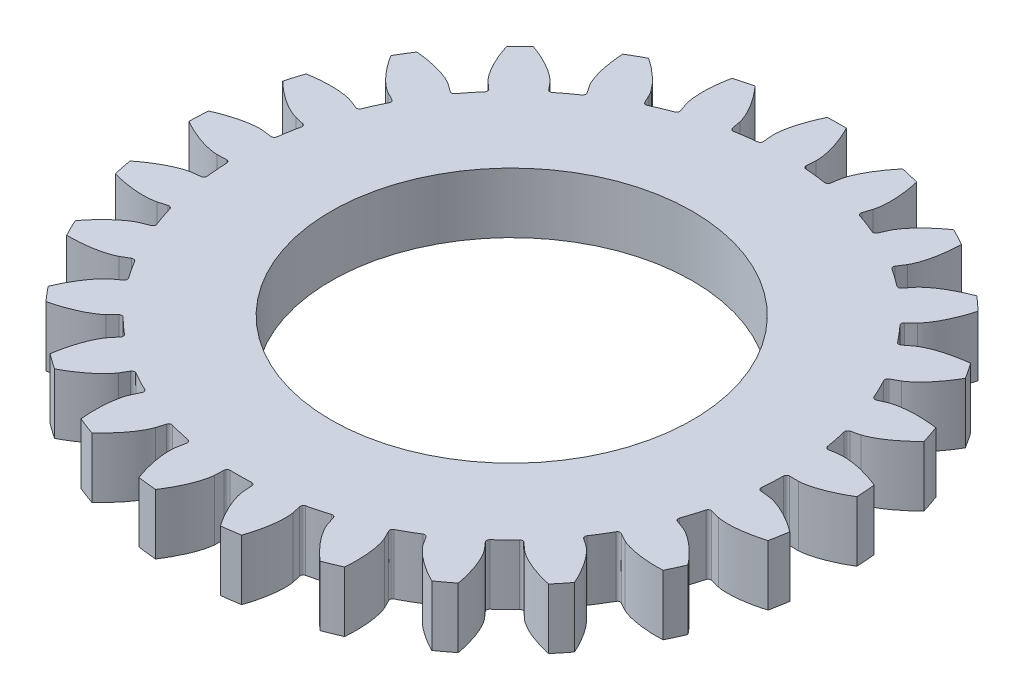
SolidWorks part; units mm, degrees
ref_plane "Front" through (0, 0, 0) normal (0, 0, 1) x (1, 0, 0)
ref_plane "Top" through (0, 0, 0) normal (0, 1, 0) x (1, 0, 0)
ref_plane "Right" through (0, 0, 0) normal (1, 0, 0) x (0, 0, -1)
sketch "Sketch3" plane through (0, 0, 0) normal (0, 1, 0) x (1, 0, 0)
  circle A0 centre (0, 0) radius 27.365
  dimension "D1" = 54.73
extrude "Boss-Extrude2" add sketch "Sketch3" against normal blind 5
sketch "Sketch4" plane through (0, 0, 0) normal (0, 1, 0) x (1, 0, 0)
  line L0 (0, 0) -> (23.8085, 0) construction
  line L1 (0, 0) -> (25.3342, 0.3427) construction
  line L2 (0, 0) -> (27.3317, -1.3487) construction
  line L3 (22.8028, 0) -> (23.8085, 0)
  line L4 (22.7751, -1.1238) -> (27.3317, -1.3487)
  circle A0 centre (0, 0) radius 25.3365
  circle A1 centre (0, 0) radius 23.8085
  circle A2 centre (0, 0) radius 22.8028
  circle A3 centre (0, 0) radius 27.365 construction
  circle A4 centre (0, 0) radius 27.365 construction
  arc A5 (27.3317, -1.3487) -> (27.3337, 1.3084) centre (0, 0) ccw
  spline S0 degree 4 poles (23.8085, 0) (23.8261, 0) (23.8755, 0.0012) (23.9687, 0.0079) (24.1203, 0.0253) (24.4006, 0.0715) (24.821, 0.17) (25.2762, 0.3139) (25.7496, 0.4971) (26.1592, 0.6786) (26.4819, 0.8345) (26.8675, 1.0357) (27.3231, 1.2956) (27.8429, 1.6229) (28.4198, 2.0263) (28.9877, 2.4636) (29.5365, 2.9252) (30.0658, 3.4083) (30.5766, 3.912) (31.0677, 4.433) (31.4823, 4.9056) (31.8241, 5.3176) (32.1044, 5.6717) (32.3185, 5.9503) (32.5396, 6.2494) (32.7342, 6.5191) (33.0063, 6.9125) (33.2008, 7.2047) (33.4934, 7.6571) (33.5905, 7.8234) (33.6939, 7.9901) knots 0 0 0 0 0 0.005377 0.015084 0.028532 0.04661 0.092111 0.146842 0.174209 0.201575 0.228941 0.256307 0.307035 0.361767 0.4165 0.471232 0.525964 0.580697 0.635429 0.690161 0.744894 0.77226 0.799626 0.826992 0.854358 0.881725 0.909091 0.954545 1 1 1 1 1 construction
  spline S1 degree 4 poles (23.8085, 0) (23.8261, 0) (23.8755, 0.0012) (23.9687, 0.0079) (24.1203, 0.0253) (24.4006, 0.0715) (24.821, 0.17) (25.2762, 0.3139) (25.7496, 0.4971) (26.1592, 0.6786) (26.4819, 0.8345) (26.8675, 1.0357) (27.3231, 1.2956) (27.8429, 1.6229) (28.4198, 2.0263) (28.9877, 2.4636) (29.5365, 2.9252) (30.0658, 3.4083) (30.5766, 3.912) (31.0677, 4.433) (31.4823, 4.9056) (31.8241, 5.3176) (32.1044, 5.6717) (32.3185, 5.9503) (32.5396, 6.2494) (32.7342, 6.5191) (32.9093, 6.7723) (33.0022, 6.9089) (33.0476, 6.9765) knots 0 0 0 0 0 0.005377 0.015084 0.028532 0.04661 0.092111 0.146842 0.174209 0.201575 0.228941 0.256307 0.307035 0.361767 0.4165 0.471232 0.525964 0.580697 0.635429 0.690161 0.744894 0.77226 0.799626 0.826992 0.854358 0.881725 0.909091 0.909091 0.909091 0.909091 0.909091
  circle M5 centre (0, 0) radius 27.365
  dimension "D1" = 50.673
  dimension "D2" = 47.617
  dimension "D3" = 45.6057
  dimension "D4" = 3.6
extrude "Cut-Extrude1" cut sketch "Sketch4" against normal blind 5 contours A2 L4 A1 L3 | S1 A1 L4 A0 | S1 A0 L4 M5
fillet "Fillet1" radius 0.2534 1 edges at (22.8028, -2.5, 0)
ref_plane "Plane2" through (0, 0, 0) normal (0.0493, 0, -0.9988) x (-0.9988, 0, -0.0493)
mirror "Mirror2" about plane through (0, 0, 0) normal (0.0493, 0, -0.9988) of "Cut-Extrude1", "Fillet1"
sketch "Sketch5" plane through (0, 0, 0) normal (0, 1, 0) x (1, 0, 0)
  line L0 (22.9428, -2.2698) -> (23.6929, -2.344) construction
  line L1 (23.0548, 0) -> (23.8085, 0) construction
  line L2 (22.9428, -2.2698) -> (23.6929, -2.344)
  line L3 (23.0548, 0) -> (23.8085, 0)
  line L4 (21.6576, -7.9041) -> (22.3656, -8.1625)
  line L5 (22.3305, -5.7335) -> (23.0605, -5.9209)
  line L6 (19.0115, -13.0418) -> (19.633, -13.4682)
  line L7 (20.2031, -11.1067) -> (20.8636, -11.4698)
  line L8 (15.1708, -17.36) -> (15.6668, -17.9276)
  line L9 (16.8062, -15.7821) -> (17.3557, -16.2981)
  line L10 (10.377, -20.5875) -> (10.7162, -21.2605)
  line L11 (12.3534, -19.4658) -> (12.7572, -20.1022)
  line L12 (4.9311, -22.5213) -> (5.0923, -23.2576)
  line L13 (7.1243, -21.9264) -> (7.3572, -22.6433)
  line L14 (-0.8247, -23.0401) -> (-0.8516, -23.7933)
  line L15 (1.4476, -23.0093) -> (1.4949, -23.7615)
  line L16 (-6.5286, -22.1111) -> (-6.742, -22.834)
  line L17 (-4.32, -22.6465) -> (-4.4613, -23.3868)
  line L18 (-11.8223, -19.7929) -> (-12.2088, -20.4399)
  line L19 (-9.8163, -20.8606) -> (-10.1372, -21.5426)
  line L20 (-16.3732, -16.2309) -> (-16.9085, -16.7616)
  line L21 (-14.6957, -17.764) -> (-15.1761, -18.3448)
  line L22 (-19.8953, -11.6492) -> (-20.5457, -12.03)
  line L23 (-18.6517, -13.5513) -> (-19.2615, -13.9943)
  line L24 (-22.1672, -6.3354) -> (-22.8919, -6.5426)
  line L25 (-21.4358, -8.487) -> (-22.1366, -8.7645)
  line L26 (-23.0464, -0.6236) -> (-23.7998, -0.644)
  line L27 (-22.873, -2.8895) -> (-23.6208, -2.984)
  line L28 (-22.4774, 5.1274) -> (-23.2123, 5.295)
  line L29 (-22.873, 2.8895) -> (-23.6208, 2.984)
  line L30 (-20.4961, 10.5562) -> (-21.1662, 10.9013)
  line L31 (-21.4358, 8.487) -> (-22.1366, 8.7645)
  line L32 (-17.227, 15.3217) -> (-17.7902, 15.8226)
  line L33 (-18.6517, 13.5513) -> (-19.2615, 13.9943)
  line L34 (-12.8754, 19.1245) -> (-13.2963, 19.7498)
  line L35 (-14.6957, 17.764) -> (-15.1761, 18.3448)
  line L36 (-7.7148, 21.7257) -> (-7.967, 22.436)
  line L37 (-9.8163, 20.8606) -> (-10.1372, 21.5426)
  line L38 (-2.0695, 22.9618) -> (-2.1372, 23.7124)
  line L39 (-4.32, 22.6465) -> (-4.4613, 23.3868)
  line L40 (3.7059, 22.755) -> (3.827, 23.4989)
  line L41 (1.4476, 23.0093) -> (1.4949, 23.7615)
  line L42 (9.2484, 21.1185) -> (9.5507, 21.8089)
  line L43 (7.1243, 21.9264) -> (7.3572, 22.6433)
  line L44 (14.2098, 18.1551) -> (14.6743, 18.7486)
  line L45 (12.3534, 19.4658) -> (12.7572, 20.1022)
  line L46 (18.2784, 14.0509) -> (18.8759, 14.5102)
  line L47 (16.8062, 15.7821) -> (17.3557, 16.2981)
  line L48 (21.1984, 9.0638) -> (21.8914, 9.3601)
  line L49 (20.2031, 11.1067) -> (20.8636, 11.4698)
  line L50 (22.7865, 3.5072) -> (23.5314, 3.6219)
  line L51 (22.3305, 5.7335) -> (23.0605, 5.9209)
  arc A0 (22.7154, -1.9955) -> (22.9428, -2.2698) centre (22.9678, -2.0176) ccw construction
  arc A1 (23.0548, 0) -> (22.8015, -0.2506) centre (23.0548, -0.2534) ccw construction
  arc A2 (22.7154, -1.9955) -> (22.8015, -0.2506) centre (0, 0) ccw construction
  arc A3 (22.7154, -1.9955) -> (22.9428, -2.2698) centre (22.9678, -2.0176) ccw
  arc A4 (23.0548, 0) -> (22.8015, -0.2506) centre (23.0548, -0.2534) ccw
  arc A5 (22.7154, -1.9955) -> (22.8015, -0.2506) centre (0, 0) ccw
  arc A6 (21.5055, -7.5818) -> (21.6576, -7.9041) centre (21.7444, -7.6661) ccw
  arc A7 (21.5055, -7.5818) -> (22.0228, -5.9132) centre (0, 0) ccw
  arc A8 (22.3305, -5.7335) -> (22.0228, -5.9132) centre (22.2675, -5.9789) ccw
  arc A9 (18.9443, -12.6918) -> (19.0115, -13.0418) centre (19.1548, -12.8329) ccw
  arc A10 (18.9443, -12.6918) -> (19.8604, -11.2043) centre (0, 0) ccw
  arc A11 (20.2031, -11.1067) -> (19.8604, -11.2043) centre (20.081, -11.3288) ccw
  arc A12 (15.1928, -17.0044) -> (15.1708, -17.36) centre (15.3616, -17.1933) ccw
  arc A13 (15.1928, -17.0044) -> (16.45, -15.7913) centre (0, 0) ccw
  arc A14 (16.8062, -15.7821) -> (16.45, -15.7913) centre (16.6328, -15.9668) ccw
  arc A15 (10.4867, -20.2484) -> (10.377, -20.5875) centre (10.6032, -20.4734) ccw
  arc A16 (10.4867, -20.2484) -> (12.0061, -19.3862) centre (0, 0) ccw
  arc A17 (12.3534, -19.4658) -> (12.0061, -19.3862) centre (12.1395, -19.6016) ccw
  arc A18 (5.1216, -22.2202) -> (4.9311, -22.5213) centre (5.1786, -22.4671) ccw
  arc A19 (5.1216, -22.2202) -> (6.8077, -21.7629) centre (0, 0) ccw
  arc A20 (7.1243, -21.9264) -> (6.8077, -21.7629) centre (6.8834, -22.0047) ccw
  arc A21 (-0.5652, -22.7958) -> (-0.8247, -23.0401) centre (-0.5715, -23.0491) ccw
  arc A22 (-0.5652, -22.7958) -> (1.1816, -22.7722) centre (0, 0) ccw
  arc A23 (1.4476, -23.0093) -> (1.1816, -22.7722) centre (1.1948, -23.0252) ccw
  arc A24 (-6.2165, -21.9391) -> (-6.5286, -22.1111) centre (-6.2856, -22.1829) ccw
  arc A25 (-6.2165, -21.9391) -> (-4.5187, -22.3506) centre (0, 0) ccw
  arc A26 (-4.32, -22.6465) -> (-4.5187, -22.3506) centre (-4.5689, -22.599) ccw
  arc A27 (-11.4773, -19.7039) -> (-11.8223, -19.7929) centre (-11.6048, -19.9228) ccw
  arc A28 (-11.4773, -19.7039) -> (-9.9351, -20.5247) centre (0, 0) ccw
  arc A29 (-9.8163, -20.8606) -> (-9.9351, -20.5247) centre (-10.0455, -20.7527) ccw
  arc A30 (-16.0168, -16.2305) -> (-16.3732, -16.2309) centre (-16.1948, -16.4109) ccw
  arc A31 (-16.0168, -16.2305) -> (-14.7273, -17.4091) centre (0, 0) ccw
  arc A32 (-14.6957, -17.764) -> (-14.7273, -17.4091) centre (-14.8909, -17.6025) ccw
  arc A33 (-19.55, -11.7374) -> (-19.8953, -11.6492) centre (-19.7672, -11.8678) ccw
  arc A34 (-19.55, -11.7374) -> (-18.5941, -13.1996) centre (0, 0) ccw
  arc A35 (-18.6517, -13.5513) -> (-18.5941, -13.1996) centre (-18.8007, -13.3463) ccw
  arc A36 (-21.8548, -6.5068) -> (-22.1672, -6.3354) centre (-22.0976, -6.5791) ccw
  arc A37 (-21.8548, -6.5068) -> (-21.2925, -8.1608) centre (0, 0) ccw
  arc A38 (-21.4358, -8.487) -> (-21.2925, -8.1608) centre (-21.5291, -8.2515) ccw
  arc A39 (-22.7864, -0.8673) -> (-23.0464, -0.6236) centre (-23.0395, -0.8769) ccw
  arc A40 (-22.7864, -0.8673) -> (-22.6531, -2.6092) centre (0, 0) ccw
  arc A41 (-22.873, -2.8895) -> (-22.6531, -2.6092) centre (-22.9048, -2.6382) ccw
  arc A42 (-22.2862, 4.8267) -> (-22.4774, 5.1274) centre (-22.5338, 4.8803) ccw
  arc A43 (-22.2862, 4.8267) -> (-22.5903, 3.1064) centre (0, 0) ccw
  arc A44 (-22.873, 2.8895) -> (-22.5903, 3.1064) centre (-22.8413, 3.1409) ccw
  arc A45 (-20.3856, 10.2174) -> (-20.4961, 10.5562) centre (-20.6122, 10.3309) ccw
  arc A46 (-20.3856, 10.2174) -> (-21.108, 8.6268) centre (0, 0) ccw
  arc A47 (-21.4358, 8.487) -> (-21.108, 8.6268) centre (-21.3426, 8.7226) ccw
  arc A48 (-17.2042, 14.9661) -> (-17.227, 15.3217) centre (-17.3954, 15.1324) ccw
  arc A49 (-17.2042, 14.9661) -> (-18.2995, 13.6051) centre (0, 0) ccw
  arc A50 (-18.6517, 13.5513) -> (-18.2995, 13.6051) centre (-18.5028, 13.7563) ccw
  arc A51 (-12.9418, 18.7744) -> (-12.8754, 19.1245) centre (-13.0856, 18.983) ccw
  arc A52 (-12.9418, 18.7744) -> (-14.3411, 17.7286) centre (0, 0) ccw
  arc A53 (-14.6957, 17.764) -> (-14.3411, 17.7286) centre (-14.5005, 17.9255) ccw
  arc A54 (-7.8662, 21.4031) -> (-7.7148, 21.7257) centre (-7.9536, 21.6409) ccw
  arc A55 (-7.8662, 21.4031) -> (-9.4817, 20.7381) centre (0, 0) ccw
  arc A56 (-9.8163, 20.8606) -> (-9.4817, 20.7381) centre (-9.587, 20.9685) ccw
  arc A57 (-2.2963, 22.6869) -> (-2.0695, 22.9618) centre (-2.3218, 22.939) ccw
  arc A58 (-2.2963, 22.6869) -> (-4.0264, 22.4446) centre (0, 0) ccw
  arc A59 (-4.32, 22.6465) -> (-4.0264, 22.4446) centre (-4.0712, 22.6939) ccw
  arc A60 (3.4178, 22.5453) -> (3.7059, 22.755) centre (3.4558, 22.7958) ccw
  arc A61 (3.4178, 22.5453) -> (1.6818, 22.7407) centre (0, 0) ccw
  arc A62 (1.4476, 23.0093) -> (1.6818, 22.7407) centre (1.7005, 22.9934) ccw
  arc A63 (8.9172, 20.987) -> (9.2484, 21.1185) centre (9.0163, 21.2202) ccw
  arc A64 (8.9172, 20.987) -> (7.2844, 21.6081) centre (0, 0) ccw
  arc A65 (7.1243, 21.9264) -> (7.2844, 21.6081) centre (7.3653, 21.8481) ccw
  arc A66 (13.8563, 18.11) -> (14.2098, 18.1551) centre (14.0103, 18.3112) ccw
  arc A67 (13.8563, 18.11) -> (12.4292, 19.1177) centre (0, 0) ccw
  arc A68 (12.3534, 19.4658) -> (12.4292, 19.1177) centre (12.5673, 19.3301) ccw
  arc A69 (17.9248, 14.0951) -> (18.2784, 14.0509) centre (18.1239, 14.2517) ccw
  arc A70 (17.9248, 14.0951) -> (16.7931, 15.426) centre (0, 0) ccw
  arc A71 (16.8062, 15.7821) -> (16.7931, 15.426) centre (16.9797, 15.5974) ccw
  arc A72 (20.8669, 9.1946) -> (21.1984, 9.0638) centre (21.0988, 9.2967) ccw
  arc A73 (20.8669, 9.1946) -> (20.1018, 10.7651) centre (0, 0) ccw
  arc A74 (20.2031, 11.1067) -> (20.1018, 10.7651) centre (20.3252, 10.8847) ccw
  arc A75 (22.498, 3.7163) -> (22.7865, 3.5072) centre (22.748, 3.7576) ccw
  arc A76 (22.498, 3.7163) -> (22.1474, 5.4278) centre (0, 0) ccw
  arc A77 (22.3305, 5.7335) -> (22.1474, 5.4278) centre (22.3935, 5.4881) ccw
  arc A78 (20.8211, -17.7574) -> (17.0012, -21.443) centre (0, 0) cw
  arc A79 (15.7509, -22.3775) -> (11.1345, -24.9973) centre (0, 0) cw
  arc A80 (26.8004, -5.5303) -> (25.2285, -10.6002) centre (0, 0) cw
  arc A81 (24.5831, -12.0215) -> (21.779, -16.5686) centre (0, 0) cw
  arc A82 (9.691, -25.5916) -> (4.5681, -26.981) centre (0, 0) cw
  arc A83 (3.0222, -27.1976) -> (-2.2854, -27.2694) centre (0, 0) cw
  arc A84 (-3.8366, -27.0947) -> (-8.9952, -25.8443) centre (0, 0) cw
  arc A85 (-10.4542, -25.2894) -> (-15.1398, -22.7954) centre (0, 0) cw
  arc A86 (-16.415, -21.895) -> (-20.3331, -18.3141) centre (0, 0) cw
  arc A87 (-21.3443, -17.1249) -> (-24.2489, -12.6821) centre (0, 0) cw
  arc A88 (-24.9326, -11.2788) -> (-26.641, -6.2532) centre (0, 0) cw
  arc A89 (-26.9542, -4.7239) -> (-27.3591, 0.5686) centre (0, 0) cw
  arc A90 (-27.2822, 2.1277) -> (-26.3582, 7.3547) centre (0, 0) cw
  arc A91 (-25.8959, 8.8456) -> (-23.701, 13.6786) centre (0, 0) cw
  arc A92 (-22.8825, 15.0078) -> (-19.5547, 19.1431) centre (0, 0) cw
  arc A93 (-18.4313, 20.2269) -> (-14.1797, 23.4047) centre (0, 0) cw
  arc A94 (-12.822, 24.1752) -> (-7.9137, 26.1957) centre (0, 0) cw
  arc A95 (-6.4071, 26.6044) -> (-1.1504, 27.3408) centre (0, 0) cw
  arc A96 (0.4104, 27.3619) -> (5.6851, 26.7679) centre (0, 0) cw
  arc A97 (7.2022, 26.4002) -> (12.1634, 24.5132) centre (0, 0) cw
  arc A98 (13.5414, 23.7797) -> (17.8774, 20.7181) centre (0, 0) cw
  arc A99 (19.0297, 19.665) -> (22.4682, 15.6213) centre (0, 0) cw
  arc A100 (23.3224, 14.3147) -> (25.6472, 9.5429) centre (0, 0) cw
  arc A101 (26.1496, 8.065) -> (27.2146, 2.8649) centre (0, 0) cw
  spline S0 degree 4 poles (-214.2368, -2992.2325) (15.1767, -47.6522) (20.52, -2.879) (22.3515, -2.0429) (24.0007, -2.3999) (24.275, -2.4734) (24.6836, -2.6128) (25.1225, -2.8008) (25.5755, -3.0298) (25.9653, -3.2507) (26.2711, -3.4376) (38.9732, -11.7519) (37.8122, -40.4808) (34.0439, 34.7604) (413.935, -2978.8727) knots -0.46871 -0.46871 -0.46871 -0.46871 -0.46871 0.005377 0.015084 0.028532 0.04661 0.092111 0.146842 0.174209 0.201575 0.228941 0.256307 4.811004 4.811004 4.811004 4.811004 4.811004 only from (23.6929, -2.344) to (27.0721, -3.9931) construction
  spline S1 degree 4 poles (81.3908, 2998.7878) (19.7944, 45.9266) (20.7038, 0.8448) (22.444, -0.1675) (24.1203, 0.0253) (24.4006, 0.0715) (24.821, 0.17) (25.2762, 0.3139) (25.7496, 0.4971) (26.1592, 0.6786) (26.4819, 0.8345) (39.9409, 7.8579) (41.6139, 36.5615) (30.4564, -37.9431) (705.1957, 2923.649) knots -0.46871 -0.46871 -0.46871 -0.46871 -0.46871 0.005377 0.015084 0.028532 0.04661 0.092111 0.146842 0.174209 0.201575 0.228941 0.256307 4.811004 4.811004 4.811004 4.811004 4.811004 only from (23.8085, 0) to (27.3337, 1.3084) construction
  spline S2 degree 4 poles (23.6929, -2.344) (23.7104, -2.3457) (23.7594, -2.3517) (23.8515, -2.3676) (24.0007, -2.3999) (24.275, -2.4734) (24.6836, -2.6128) (25.1225, -2.8008) (25.5755, -3.0298) (25.9653, -3.2507) (26.3644, -3.4947) (26.6783, -3.7058) (26.9128, -3.874) (27.0721, -3.9931) knots 0 0 0 0 0 0.005377 0.015084 0.028532 0.04661 0.092111 0.146842 0.174209 0.201575 0.228941 0.289708 0.289708 0.289708 0.289708 0.289708
  spline S3 degree 4 poles (23.8085, 0) (23.8261, 0) (23.8755, 0.0012) (23.9687, 0.0079) (24.1203, 0.0253) (24.4006, 0.0715) (24.821, 0.17) (25.2762, 0.3139) (25.7496, 0.4971) (26.1592, 0.6786) (26.5804, 0.8821) (26.9135, 1.0613) (27.1634, 1.2056) (27.3337, 1.3084) knots 0 0 0 0 0 0.005377 0.015084 0.028532 0.04661 0.092111 0.146842 0.174209 0.201575 0.228941 0.289708 0.289708 0.289708 0.289708 0.289708
  spline S4 degree 4 poles (22.3656, -8.1625) (22.3821, -8.1685) (22.4281, -8.1865) (22.5134, -8.2248) (22.6498, -8.2932) (22.8973, -8.4327) (23.2584, -8.6693) (23.6367, -8.9605) (24.0186, -9.295) (24.3411, -9.6059) (24.667, -9.9414) (24.9185, -10.224) (25.1038, -10.4452) (25.2285, -10.6002) knots 0 0 0 0 0 0.005377 0.015084 0.028532 0.04661 0.092111 0.146842 0.174209 0.201575 0.228941 0.289708 0.289708 0.289708 0.289708 0.289708
  spline S5 degree 4 poles (23.0605, -5.9209) (23.0776, -5.9253) (23.1257, -5.9365) (23.2177, -5.9531) (23.3688, -5.974) (23.6518, -5.9989) (24.0835, -6.008) (24.5602, -5.9819) (25.0642, -5.9222) (25.5061, -5.8482) (25.9647, -5.7559) (26.3319, -5.6652) (26.6099, -5.5875) (26.8004, -5.5303) knots 0 0 0 0 0 0.005377 0.015084 0.028532 0.04661 0.092111 0.146842 0.174209 0.201575 0.228941 0.289708 0.289708 0.289708 0.289708 0.289708
  spline S6 degree 4 poles (19.633, -13.4682) (19.6475, -13.4783) (19.6874, -13.5076) (19.7601, -13.5666) (19.8747, -13.6681) (20.0786, -13.867) (20.3675, -14.1895) (20.6591, -14.5692) (20.9429, -14.9918) (21.1754, -15.3762) (21.4047, -15.7855) (21.5756, -16.1241) (21.6981, -16.3863) (21.779, -16.5686) knots 0 0 0 0 0 0.005377 0.015084 0.028532 0.04661 0.092111 0.146842 0.174209 0.201575 0.228941 0.289708 0.289708 0.289708 0.289708 0.289708
  spline S7 degree 4 poles (20.8636, -11.4698) (20.879, -11.4783) (20.9228, -11.5011) (21.0077, -11.5401) (21.149, -11.5979) (21.4169, -11.6924) (21.8327, -11.8086) (22.3009, -11.9019) (22.804, -11.9693) (23.2504, -12.0076) (23.7175, -12.0322) (24.0958, -12.0357) (24.3843, -12.0296) (24.5831, -12.0215) knots 0 0 0 0 0 0.005377 0.015084 0.028532 0.04661 0.092111 0.146842 0.174209 0.201575 0.228941 0.289708 0.289708 0.289708 0.289708 0.289708
  spline S8 degree 4 poles (15.6668, -17.9276) (15.6784, -17.9408) (15.71, -17.9787) (15.7663, -18.0534) (15.8529, -18.179) (16.0026, -18.4204) (16.205, -18.8018) (16.3963, -19.2393) (16.5697, -19.7163) (16.7026, -20.1441) (16.8266, -20.5952) (16.9108, -20.9639) (16.9666, -21.2471) (17.0012, -21.443) knots 0 0 0 0 0 0.005377 0.015084 0.028532 0.04661 0.092111 0.146842 0.174209 0.201575 0.228941 0.289708 0.289708 0.289708 0.289708 0.289708
  spline S9 degree 4 poles (17.3557, -16.2981) (17.3685, -16.3101) (17.4053, -16.3431) (17.4778, -16.402) (17.6003, -16.493) (17.8362, -16.6513) (18.2101, -16.8672) (18.6404, -17.074) (19.1109, -17.2644) (19.5338, -17.4125) (19.9801, -17.5525) (20.3456, -17.6499) (20.6266, -17.7158) (20.8211, -17.7574) knots 0 0 0 0 0 0.005377 0.015084 0.028532 0.04661 0.092111 0.146842 0.174209 0.201575 0.228941 0.289708 0.289708 0.289708 0.289708 0.289708
  spline S10 degree 4 poles (10.7162, -21.2605) (10.7241, -21.2762) (10.7453, -21.3208) (10.7813, -21.4071) (10.8339, -21.5503) (10.9189, -21.8214) (11.0201, -22.2411) (11.0965, -22.7124) (11.1459, -23.2176) (11.1683, -23.665) (11.1761, -24.1328) (11.166, -24.5109) (11.1497, -24.799) (11.1345, -24.9973) knots 0 0 0 0 0 0.005377 0.015084 0.028532 0.04661 0.092111 0.146842 0.174209 0.201575 0.228941 0.289708 0.289708 0.289708 0.289708 0.289708
  spline S11 degree 4 poles (12.7572, -20.1022) (12.7667, -20.1171) (12.7941, -20.1581) (12.8497, -20.2332) (12.9457, -20.3519) (13.1349, -20.5638) (13.4433, -20.8659) (13.8087, -21.1733) (14.217, -21.4747) (14.5898, -21.7233) (14.9873, -21.9699) (15.3171, -22.1552) (15.5728, -22.2888) (15.7509, -22.3775) knots 0 0 0 0 0 0.005377 0.015084 0.028532 0.04661 0.092111 0.146842 0.174209 0.201575 0.228941 0.289708 0.289708 0.289708 0.289708 0.289708
  spline S12 degree 4 poles (5.0923, -23.2576) (5.096, -23.2748) (5.1055, -23.3232) (5.1188, -23.4157) (5.1342, -23.5676) (5.1491, -23.8513) (5.1427, -24.283) (5.0996, -24.7585) (5.0218, -25.26) (4.9321, -25.699) (4.8234, -26.154) (4.7196, -26.5177) (4.6321, -26.7927) (4.5681, -26.981) knots 0 0 0 0 0 0.005377 0.015084 0.028532 0.04661 0.092111 0.146842 0.174209 0.201575 0.228941 0.289708 0.289708 0.289708 0.289708 0.289708
  spline S13 degree 4 poles (7.3572, -22.6433) (7.3627, -22.66) (7.379, -22.7066) (7.4142, -22.7932) (7.4777, -22.932) (7.6082, -23.1843) (7.8318, -23.5536) (8.1093, -23.9421) (8.4298, -24.3357) (8.729, -24.6692) (9.0527, -25.0069) (9.3261, -25.2683) (9.5405, -25.4614) (9.691, -25.5916) knots 0 0 0 0 0 0.005377 0.015084 0.028532 0.04661 0.092111 0.146842 0.174209 0.201575 0.228941 0.289708 0.289708 0.289708 0.289708 0.289708
  spline S14 degree 4 poles (-0.8516, -23.7933) (-0.8523, -23.8109) (-0.8552, -23.8602) (-0.8653, -23.9531) (-0.8881, -24.104) (-0.9443, -24.3824) (-1.0578, -24.799) (-1.2178, -25.2488) (-1.4179, -25.7153) (-1.6139, -26.1182) (-1.8323, -26.5318) (-2.0233, -26.8583) (-2.1765, -27.1029) (-2.2854, -27.2694) knots 0 0 0 0 0 0.005377 0.015084 0.028532 0.04661 0.092111 0.146842 0.174209 0.201575 0.228941 0.289708 0.289708 0.289708 0.289708 0.289708
  spline S15 degree 4 poles (1.4949, -23.7615) (1.4961, -23.7791) (1.5003, -23.8283) (1.5129, -23.9209) (1.5398, -24.0711) (1.6035, -24.348) (1.7282, -24.7613) (1.9004, -25.2067) (2.113, -25.6675) (2.3198, -26.065) (2.5494, -26.4726) (2.7491, -26.7938) (2.9088, -27.0341) (3.0222, -27.1976) knots 0 0 0 0 0 0.005377 0.015084 0.028532 0.04661 0.092111 0.146842 0.174209 0.201575 0.228941 0.289708 0.289708 0.289708 0.289708 0.289708
  spline S16 degree 4 poles (-6.742, -22.834) (-6.747, -22.8509) (-6.7621, -22.8979) (-6.795, -22.9854) (-6.8546, -23.1259) (-6.9783, -23.3816) (-7.1918, -23.7568) (-7.4587, -24.1527) (-7.7685, -24.5548) (-8.0585, -24.8963) (-8.373, -25.2426) (-8.6392, -25.5113) (-8.8483, -25.7102) (-8.9952, -25.8443) knots 0 0 0 0 0 0.005377 0.015084 0.028532 0.04661 0.092111 0.146842 0.174209 0.201575 0.228941 0.289708 0.289708 0.289708 0.289708 0.289708
  spline S17 degree 4 poles (-4.4613, -23.3868) (-4.4646, -23.4041) (-4.4727, -23.4528) (-4.4835, -23.5456) (-4.4948, -23.6978) (-4.502, -23.9818) (-4.484, -24.4132) (-4.428, -24.8873) (-4.3367, -25.3866) (-4.2352, -25.823) (-4.1142, -26.2749) (-4.0006, -26.6357) (-3.9057, -26.9082) (-3.8366, -27.0947) knots 0 0 0 0 0 0.005377 0.015084 0.028532 0.04661 0.092111 0.146842 0.174209 0.201575 0.228941 0.289708 0.289708 0.289708 0.289708 0.289708
  spline S18 degree 4 poles (-12.2088, -20.4399) (-12.2178, -20.455) (-12.2441, -20.4968) (-12.2977, -20.5734) (-12.3904, -20.6946) (-12.5738, -20.9116) (-12.874, -21.2219) (-13.2309, -21.539) (-13.6309, -21.8514) (-13.9968, -22.11) (-14.3875, -22.3673) (-14.7122, -22.5614) (-14.9642, -22.7019) (-15.1398, -22.7954) knots 0 0 0 0 0 0.005377 0.015084 0.028532 0.04661 0.092111 0.146842 0.174209 0.201575 0.228941 0.289708 0.289708 0.289708 0.289708 0.289708
  spline S19 degree 4 poles (-10.1372, -21.5426) (-10.1447, -21.5585) (-10.1646, -21.6037) (-10.1982, -21.6909) (-10.247, -21.8355) (-10.3246, -22.1088) (-10.4144, -22.5311) (-10.4781, -23.0043) (-10.5138, -23.5106) (-10.524, -23.9585) (-10.5192, -24.4262) (-10.4989, -24.8039) (-10.4748, -25.0915) (-10.4542, -25.2894) knots 0 0 0 0 0 0.005377 0.015084 0.028532 0.04661 0.092111 0.146842 0.174209 0.201575 0.228941 0.289708 0.289708 0.289708 0.289708 0.289708
  spline S20 degree 4 poles (-16.9085, -16.7616) (-16.921, -16.774) (-16.9568, -16.8079) (-17.0278, -16.8687) (-17.1477, -16.9631) (-17.3793, -17.1276) (-17.7472, -17.3536) (-18.1718, -17.572) (-18.6369, -17.775) (-19.0556, -17.9345) (-19.498, -18.0865) (-19.8607, -18.1938) (-20.1398, -18.2673) (-20.3331, -18.3141) knots 0 0 0 0 0 0.005377 0.015084 0.028532 0.04661 0.092111 0.146842 0.174209 0.201575 0.228941 0.289708 0.289708 0.289708 0.289708 0.289708
  spline S21 degree 4 poles (-15.1761, -18.3448) (-15.1873, -18.3583) (-15.2179, -18.3971) (-15.2722, -18.4732) (-15.3554, -18.6012) (-15.4985, -18.8466) (-15.6905, -19.2333) (-15.8698, -19.6757) (-16.0304, -20.1573) (-16.1516, -20.5886) (-16.2633, -21.0428) (-16.3376, -21.4137) (-16.3857, -21.6983) (-16.415, -21.895) knots 0 0 0 0 0 0.005377 0.015084 0.028532 0.04661 0.092111 0.146842 0.174209 0.201575 0.228941 0.289708 0.289708 0.289708 0.289708 0.289708
  spline S22 degree 4 poles (-20.5457, -12.03) (-20.5609, -12.0389) (-20.604, -12.0629) (-20.6879, -12.1041) (-20.8275, -12.1657) (-21.0928, -12.2675) (-21.5053, -12.3949) (-21.9708, -12.5008) (-22.4719, -12.5818) (-22.9171, -12.6322) (-23.3834, -12.6694) (-23.7614, -12.6831) (-24.05, -12.6848) (-24.2489, -12.6821) knots 0 0 0 0 0 0.005377 0.015084 0.028532 0.04661 0.092111 0.146842 0.174209 0.201575 0.228941 0.289708 0.289708 0.289708 0.289708 0.289708
  spline S23 degree 4 poles (-19.2615, -13.9943) (-19.2757, -14.0046) (-19.315, -14.0346) (-19.3865, -14.0948) (-19.4989, -14.1981) (-19.6985, -14.4002) (-19.9806, -14.727) (-20.2644, -15.1109) (-20.5396, -15.5374) (-20.7644, -15.925) (-20.9855, -16.3372) (-21.1497, -16.678) (-21.267, -16.9416) (-21.3443, -17.1249) knots 0 0 0 0 0 0.005377 0.015084 0.028532 0.04661 0.092111 0.146842 0.174209 0.201575 0.228941 0.289708 0.289708 0.289708 0.289708 0.289708
  spline S24 degree 4 poles (-22.8919, -6.5426) (-22.9089, -6.5474) (-22.9566, -6.5599) (-23.0481, -6.579) (-23.1987, -6.6039) (-23.4809, -6.6365) (-23.9121, -6.6573) (-24.3894, -6.6441) (-24.8949, -6.598) (-25.3386, -6.5361) (-25.7995, -6.4561) (-26.169, -6.3754) (-26.449, -6.3053) (-26.641, -6.2532) knots 0 0 0 0 0 0.005377 0.015084 0.028532 0.04661 0.092111 0.146842 0.174209 0.201575 0.228941 0.289708 0.289708 0.289708 0.289708 0.289708
  spline S25 degree 4 poles (-22.1366, -8.7645) (-22.153, -8.771) (-22.1984, -8.7902) (-22.2826, -8.8308) (-22.4172, -8.9028) (-22.6608, -9.0489) (-23.0154, -9.2953) (-23.3857, -9.5966) (-23.7583, -9.9413) (-24.0724, -10.2608) (-24.3891, -10.6051) (-24.6329, -10.8943) (-24.8121, -11.1205) (-24.9326, -11.2788) knots 0 0 0 0 0 0.005377 0.015084 0.028532 0.04661 0.092111 0.146842 0.174209 0.201575 0.228941 0.289708 0.289708 0.289708 0.289708 0.289708
  spline S26 degree 4 poles (-23.7998, -0.644) (-23.8174, -0.6445) (-23.8668, -0.6447) (-23.9602, -0.6405) (-24.1122, -0.6271) (-24.3936, -0.5886) (-24.8165, -0.5014) (-25.2755, -0.37) (-25.7536, -0.1996) (-26.168, -0.0293) (-26.5945, 0.1628) (-26.9324, 0.3329) (-27.1861, 0.4704) (-27.3591, 0.5686) knots 0 0 0 0 0 0.005377 0.015084 0.028532 0.04661 0.092111 0.146842 0.174209 0.201575 0.228941 0.289708 0.289708 0.289708 0.289708 0.289708
  spline S27 degree 4 poles (-23.6208, -2.984) (-23.6383, -2.9862) (-23.6871, -2.9935) (-23.7787, -3.0119) (-23.927, -3.0482) (-24.1993, -3.1291) (-24.6039, -3.2796) (-25.0376, -3.4793) (-25.4842, -3.7205) (-25.8679, -3.9519) (-26.2602, -4.2066) (-26.5683, -4.4261) (-26.7981, -4.6006) (-26.9542, -4.7239) knots 0 0 0 0 0 0.005377 0.015084 0.028532 0.04661 0.092111 0.146842 0.174209 0.201575 0.228941 0.289708 0.289708 0.289708 0.289708 0.289708
  spline S28 degree 4 poles (-23.2123, 5.295) (-23.2294, 5.2989) (-23.2773, 5.311) (-23.3667, 5.3383) (-23.5106, 5.389) (-23.7736, 5.4964) (-24.1615, 5.6859) (-24.5734, 5.9274) (-24.9941, 6.2113) (-25.3531, 6.4794) (-25.7185, 6.7715) (-26.0034, 7.0202) (-26.215, 7.2165) (-26.3582, 7.3547) knots 0 0 0 0 0 0.005377 0.015084 0.028532 0.04661 0.092111 0.146842 0.174209 0.201575 0.228941 0.289708 0.289708 0.289708 0.289708 0.289708
  spline S29 degree 4 poles (-23.6208, 2.984) (-23.6383, 2.9862) (-23.6874, 2.9912) (-23.7807, 2.9963) (-23.9333, 2.998) (-24.2172, 2.9873) (-24.6466, 2.9422) (-25.1163, 2.8566) (-25.6088, 2.7341) (-26.038, 2.6054) (-26.4814, 2.4563) (-26.8343, 2.3202) (-27.1003, 2.2084) (-27.2822, 2.1277) knots 0 0 0 0 0 0.005377 0.015084 0.028532 0.04661 0.092111 0.146842 0.174209 0.201575 0.228941 0.289708 0.289708 0.289708 0.289708 0.289708
  spline S30 degree 4 poles (-21.1662, 10.9013) (-21.1818, 10.9093) (-21.2252, 10.933) (-21.305, 10.9816) (-21.4318, 11.0666) (-21.6598, 11.236) (-21.9884, 11.516) (-22.3273, 11.8523) (-22.6642, 12.232) (-22.9453, 12.5809) (-23.2265, 12.9547) (-23.4406, 13.2665) (-23.5967, 13.5092) (-23.701, 13.6786) knots 0 0 0 0 0 0.005377 0.015084 0.028532 0.04661 0.092111 0.146842 0.174209 0.201575 0.228941 0.289708 0.289708 0.289708 0.289708 0.289708
  spline S31 degree 4 poles (-22.1366, 8.7645) (-22.153, 8.771) (-22.1993, 8.7881) (-22.2884, 8.8161) (-22.4358, 8.8557) (-22.7134, 8.916) (-23.1405, 8.9791) (-23.6168, 9.013) (-24.1244, 9.0168) (-24.572, 8.9989) (-25.0385, 8.9647) (-25.4142, 8.9208) (-25.6997, 8.8786) (-25.8959, 8.8456) knots 0 0 0 0 0 0.005377 0.015084 0.028532 0.04661 0.092111 0.146842 0.174209 0.201575 0.228941 0.289708 0.289708 0.289708 0.289708 0.289708
  spline S32 degree 4 poles (-17.7902, 15.8226) (-17.8033, 15.8343) (-17.8395, 15.868) (-17.9046, 15.935) (-18.0063, 16.0488) (-18.1851, 16.2695) (-18.4337, 16.6225) (-18.6783, 17.0326) (-18.9102, 17.4841) (-19.0957, 17.8919) (-19.2751, 18.3239) (-19.405, 18.6791) (-19.4958, 18.9531) (-19.5547, 19.1431) knots 0 0 0 0 0 0.005377 0.015084 0.028532 0.04661 0.092111 0.146842 0.174209 0.201575 0.228941 0.289708 0.289708 0.289708 0.289708 0.289708
  spline S33 degree 4 poles (-19.2615, 13.9943) (-19.2757, 14.0046) (-19.3164, 14.0327) (-19.3957, 14.0821) (-19.5286, 14.1571) (-19.7825, 14.2845) (-20.1805, 14.4518) (-20.6334, 14.6031) (-21.124, 14.733) (-21.5621, 14.827) (-22.0225, 14.9099) (-22.3973, 14.9608) (-22.6843, 14.9909) (-22.8825, 15.0078) knots 0 0 0 0 0 0.005377 0.015084 0.028532 0.04661 0.092111 0.146842 0.174209 0.201575 0.228941 0.289708 0.289708 0.289708 0.289708 0.289708
  spline S34 degree 4 poles (-13.2963, 19.7498) (-13.3062, 19.7644) (-13.3328, 19.806) (-13.3793, 19.887) (-13.4495, 20.0226) (-13.5677, 20.2809) (-13.7207, 20.6846) (-13.8557, 21.1426) (-13.968, 21.6375) (-14.0462, 22.0787) (-14.1126, 22.5417) (-14.15, 22.9181) (-14.1699, 23.206) (-14.1797, 23.4047) knots 0 0 0 0 0 0.005377 0.015084 0.028532 0.04661 0.092111 0.146842 0.174209 0.201575 0.228941 0.289708 0.289708 0.289708 0.289708 0.289708
  spline S35 degree 4 poles (-15.1761, 18.3448) (-15.1873, 18.3583) (-15.2197, 18.3956) (-15.2843, 18.4632) (-15.3944, 18.5689) (-15.6086, 18.7554) (-15.9525, 19.0165) (-16.3535, 19.2756) (-16.7964, 19.5235) (-17.1974, 19.7235) (-17.6227, 19.9183) (-17.9731, 20.0607) (-18.2435, 20.1613) (-18.4313, 20.2269) knots 0 0 0 0 0 0.005377 0.015084 0.028532 0.04661 0.092111 0.146842 0.174209 0.201575 0.228941 0.289708 0.289708 0.289708 0.289708 0.289708
  spline S36 degree 4 poles (-7.967, 22.436) (-7.9729, 22.4525) (-7.9884, 22.4994) (-8.0132, 22.5895) (-8.0475, 22.7383) (-8.0978, 23.0178) (-8.1456, 23.4469) (-8.1624, 23.9241) (-8.1481, 24.4315) (-8.1142, 24.8782) (-8.0633, 25.3432) (-8.006, 25.7171) (-7.9536, 26.0009) (-7.9137, 26.1957) knots 0 0 0 0 0 0.005377 0.015084 0.028532 0.04661 0.092111 0.146842 0.174209 0.201575 0.228941 0.289708 0.289708 0.289708 0.289708 0.289708
  spline S37 degree 4 poles (-10.1372, 21.5426) (-10.1447, 21.5585) (-10.1667, 21.6027) (-10.2125, 21.6842) (-10.2929, 21.8139) (-10.454, 22.0479) (-10.7221, 22.3863) (-11.0461, 22.737) (-11.4134, 23.0872) (-11.7521, 23.3806) (-12.1155, 23.6751) (-12.4195, 23.9002) (-12.6565, 24.0649) (-12.822, 24.1752) knots 0 0 0 0 0 0.005377 0.015084 0.028532 0.04661 0.092111 0.146842 0.174209 0.201575 0.228941 0.289708 0.289708 0.289708 0.289708 0.289708
  spline S38 degree 4 poles (-2.1372, 23.7124) (-2.1387, 23.7299) (-2.142, 23.7792) (-2.1437, 23.8727) (-2.1399, 24.0252) (-2.1191, 24.3085) (-2.0587, 24.736) (-1.9563, 25.2024) (-1.8163, 25.6902) (-1.6723, 26.1145) (-1.5074, 26.5523) (-1.3589, 26.9001) (-1.2376, 27.162) (-1.1504, 27.3408) knots 0 0 0 0 0 0.005377 0.015084 0.028532 0.04661 0.092111 0.146842 0.174209 0.201575 0.228941 0.289708 0.289708 0.289708 0.289708 0.289708
  spline S39 degree 4 poles (-4.4613, 23.3868) (-4.4646, 23.4041) (-4.475, 23.4524) (-4.499, 23.5427) (-4.5446, 23.6883) (-4.6425, 23.955) (-4.818, 24.3495) (-5.0446, 24.7697) (-5.3133, 25.2003) (-5.5683, 25.5687) (-5.8472, 25.9443) (-6.0856, 26.2379) (-6.2742, 26.4564) (-6.4071, 26.6044) knots 0 0 0 0 0 0.005377 0.015084 0.028532 0.04661 0.092111 0.146842 0.174209 0.201575 0.228941 0.289708 0.289708 0.289708 0.289708 0.289708
  spline S40 degree 4 poles (3.827, 23.4989) (3.8299, 23.5163) (3.8389, 23.5648) (3.8606, 23.6558) (3.9021, 23.8026) (3.9928, 24.0718) (4.1576, 24.4709) (4.3727, 24.8971) (4.6297, 25.3348) (4.8747, 25.71) (5.1432, 26.093) (5.3736, 26.3929) (5.5562, 26.6164) (5.6851, 26.7679) knots 0 0 0 0 0 0.005377 0.015084 0.028532 0.04661 0.092111 0.146842 0.174209 0.201575 0.228941 0.289708 0.289708 0.289708 0.289708 0.289708
  spline S41 degree 4 poles (1.4949, 23.7615) (1.4961, 23.7791) (1.498, 23.8285) (1.4971, 23.9219) (1.4893, 24.0743) (1.4608, 24.357) (1.3888, 24.7827) (1.2739, 25.2461) (1.1207, 25.73) (0.9653, 26.1502) (0.7886, 26.5833) (0.6307, 26.927) (0.5024, 27.1855) (0.4104, 27.3619) knots 0 0 0 0 0 0.005377 0.015084 0.028532 0.04661 0.092111 0.146842 0.174209 0.201575 0.228941 0.289708 0.289708 0.289708 0.289708 0.289708
  spline S42 degree 4 poles (9.5507, 21.8089) (9.5578, 21.8251) (9.5787, 21.8698) (9.6222, 21.9525) (9.699, 22.0844) (9.8537, 22.3226) (10.1126, 22.6681) (10.427, 23.0275) (10.7848, 23.3875) (11.1153, 23.69) (11.4707, 23.9941) (11.7685, 24.2274) (12.0009, 24.3984) (12.1634, 24.5132) knots 0 0 0 0 0 0.005377 0.015084 0.028532 0.04661 0.092111 0.146842 0.174209 0.201575 0.228941 0.289708 0.289708 0.289708 0.289708 0.289708
  spline S43 degree 4 poles (7.3572, 22.6433) (7.3627, 22.66) (7.3768, 22.7073) (7.3992, 22.798) (7.4295, 22.9476) (7.4722, 23.2285) (7.5084, 23.6587) (7.5123, 24.1361) (7.4843, 24.6429) (7.4382, 25.0886) (7.3749, 25.552) (7.3074, 25.9242) (7.2474, 26.2065) (7.2022, 26.4002) knots 0 0 0 0 0 0.005377 0.015084 0.028532 0.04661 0.092111 0.146842 0.174209 0.201575 0.228941 0.289708 0.289708 0.289708 0.289708 0.289708
  spline S44 degree 4 poles (14.6743, 18.7486) (14.6852, 18.7624) (14.7165, 18.8006) (14.7793, 18.8699) (14.8865, 18.9785) (15.0956, 19.1708) (15.4323, 19.4411) (15.8261, 19.7109) (16.2622, 19.9707) (16.6576, 20.1814) (17.0774, 20.3877) (17.4238, 20.5396) (17.6915, 20.6474) (17.8774, 20.7181) knots 0 0 0 0 0 0.005377 0.015084 0.028532 0.04661 0.092111 0.146842 0.174209 0.201575 0.228941 0.289708 0.289708 0.289708 0.289708 0.289708
  spline S45 degree 4 poles (12.7572, 20.1022) (12.7667, 20.1171) (12.7922, 20.1594) (12.8364, 20.2417) (12.9029, 20.379) (13.0141, 20.6404) (13.1562, 21.0481) (13.2787, 21.5096) (13.3776, 22.0075) (13.4438, 22.4506) (13.4977, 22.9152) (13.5249, 23.2925) (13.537, 23.5808) (13.5414, 23.7797) knots 0 0 0 0 0 0.005377 0.015084 0.028532 0.04661 0.092111 0.146842 0.174209 0.201575 0.228941 0.289708 0.289708 0.289708 0.289708 0.289708
  spline S46 degree 4 poles (18.8759, 14.5102) (18.8899, 14.5209) (18.9297, 14.5501) (19.0077, 14.6016) (19.1385, 14.6802) (19.3889, 14.8144) (19.7822, 14.9924) (20.2308, 15.1559) (20.7178, 15.2991) (21.1531, 15.4048) (21.6111, 15.5002) (21.9844, 15.5611) (22.2705, 15.599) (22.4682, 15.6213) knots 0 0 0 0 0 0.005377 0.015084 0.028532 0.04661 0.092111 0.146842 0.174209 0.201575 0.228941 0.289708 0.289708 0.289708 0.289708 0.289708
  spline S47 degree 4 poles (17.3557, 16.2981) (17.3685, 16.3101) (17.4037, 16.3447) (17.467, 16.4135) (17.5656, 16.53) (17.7383, 16.7555) (17.9773, 17.1151) (18.2107, 17.5316) (18.4303, 17.9892) (18.6047, 18.4019) (18.7724, 18.8386) (18.8926, 19.1972) (18.976, 19.4735) (19.0297, 19.665) knots 0 0 0 0 0 0.005377 0.015084 0.028532 0.04661 0.092111 0.146842 0.174209 0.201575 0.228941 0.289708 0.289708 0.289708 0.289708 0.289708
  spline S48 degree 4 poles (21.8914, 9.3601) (21.9076, 9.367) (21.9535, 9.3854) (22.0418, 9.4158) (22.1881, 9.4594) (22.464, 9.5271) (22.8892, 9.6018) (23.3644, 9.6485) (23.8716, 9.6661) (24.3196, 9.6603) (24.7869, 9.6387) (25.1636, 9.6049) (25.4501, 9.5705) (25.6472, 9.5429) knots 0 0 0 0 0 0.005377 0.015084 0.028532 0.04661 0.092111 0.146842 0.174209 0.201575 0.228941 0.289708 0.289708 0.289708 0.289708 0.289708
  spline S49 degree 4 poles (20.8636, 11.4698) (20.879, 11.4783) (20.9217, 11.5031) (21.0001, 11.5539) (21.1246, 11.6423) (21.348, 11.8177) (21.6689, 12.1066) (21.9985, 12.452) (22.325, 12.8406) (22.5966, 13.197) (22.8676, 13.5782) (23.0732, 13.8957) (23.2227, 14.1426) (23.3224, 14.3147) knots 0 0 0 0 0 0.005377 0.015084 0.028532 0.04661 0.092111 0.146842 0.174209 0.201575 0.228941 0.289708 0.289708 0.289708 0.289708 0.289708
  spline S50 degree 4 poles (23.5314, 3.6219) (23.5488, 3.6245) (23.5978, 3.6309) (23.6909, 3.6384) (23.8435, 3.6443) (24.1275, 3.6413) (24.558, 3.6078) (25.0298, 3.5349) (25.5255, 3.4258) (25.958, 3.3087) (26.4052, 3.1717) (26.7617, 3.0453) (27.0307, 2.9406) (27.2146, 2.8649) knots 0 0 0 0 0 0.005377 0.015084 0.028532 0.04661 0.092111 0.146842 0.174209 0.201575 0.228941 0.289708 0.289708 0.289708 0.289708 0.289708
  spline S51 degree 4 poles (23.0605, 5.9209) (23.0776, 5.9253) (23.1251, 5.9387) (23.2137, 5.9684) (23.3562, 6.023) (23.6163, 6.1374) (23.9989, 6.3374) (24.4041, 6.59) (24.817, 6.8852) (25.1686, 7.1628) (25.5259, 7.4647) (25.804, 7.7211) (26.0102, 7.923) (26.1496, 8.065) knots 0 0 0 0 0 0.005377 0.015084 0.028532 0.04661 0.092111 0.146842 0.174209 0.201575 0.228941 0.289708 0.289708 0.289708 0.289708 0.289708
  point P254 (0, 0)
  arc M7 (27.3337, 1.3084) -> (27.0721, -3.9931) centre (0, 0) ccw
  dimension "D1" = 25
extrude "Cut-Extrude2" cut sketch "Sketch5" against normal through all and the other way through all contours S27 L27 A41 A40 A39 L26 S26 M7 | S29 L29 A44 A43 A42 L28 S28 M7 | S31 L31 A47 A46 A45 L30 S30 M7 | S33 L33 A50 A49 A48 L32 S32 M7 | S35 L35 A53 A52 A51 L34 S34 M7 | S37 L37 A56 A55 A54 L36 S36 M7 | S39 L39 A59 A58 A57 L38 S38 M7 | S41 L41 A62 A61 A60 L40 S40 M7 | S43 L43 A65 A64 A63 L42 S42 M7 | S45 L45 A68 A67 A66 L44 S44 M7 | S47 L47 A71 A70 A69 L46 S46 M7 | S49 L49 A74 A73 A72 L48 S48 M7 | S51 L51 A77 A76 A75 L50 S50 M7 | S5 L5 A8 A7 A6 L4 S4 M7 | S7 L7 A11 A10 A9 L6 S6 M7 | S9 L9 A14 A13 A12 L8 S8 M7 | S11 L11 A17 A16 A15 L10 S10 M7 | S13 L13 A20 A19 A18 L12 S12 M7 | S15 L15 A23 A22 A21 L14 S14 M7 | S17 L17 A26 A25 A24 L16 S16 M7 | S19 L19 A29 A28 A27 L18 S18 M7 | S21 L21 A32 A31 A30 L20 S20 M7 | S23 L23 A35 A34 A33 L22 S22 M7 | S25 L25 A38 A37 A36 L24 S24 M7
sketch "Sketch6" plane through (0, 0, 0) normal (0, 1, 0) x (1, 0, 0)
  circle A0 centre (0, 0) radius 15
  dimension "D1" = 30
extrude "Cut-Extrude3" cut sketch "Sketch6" against normal through all
equation "\"t\"= 25'Teeth"
equation "\"d\"= 1.995in'Pitch circle Diameter"
equation "\"Outside Diameter\"= 2.129in"
equation "\"phi\"= 20deg'Pressure Angle"
equation "\"a\"= \"d\" / \"t\"'addendum"
equation "\"b\"= 1.25 * \"a\"'dedendum"
equation "\"c\"= \"b\" - \"a\"'Clearance"
equation "\"db\"= \"d\" * cos ( \"phi\" )'Base Circle Diameter"
equation "\"D1@Sketch4\"=\"d\""
equation "\"D3@Sketch4\"=\"d\"-2*\"b\""
equation "\"D4@Sketch4\"=360/(4*\"t\")"
equation "\"D1@Fillet1\"=\"c\"/2"
equation "\"D1@CirPattern15\"=\"t\""
